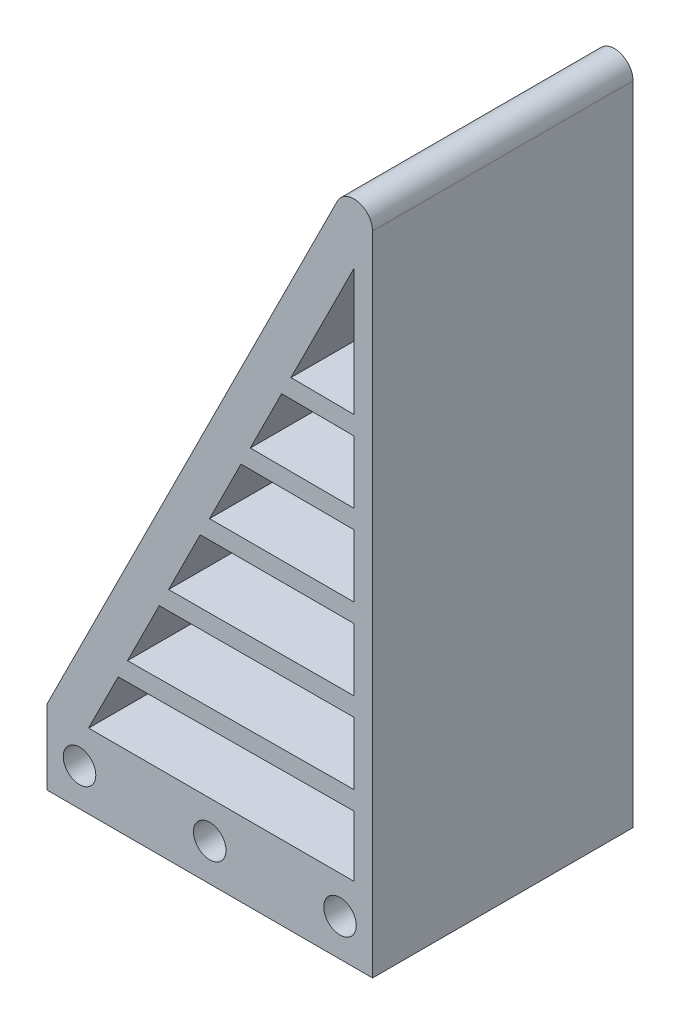
SolidWorks part; units mm, degrees
ref_plane "Спереди" through (0, 0, 0) normal (0, 0, 1) x (1, 0, 0)
ref_plane "Сверху" through (0, 0, 0) normal (0, 1, 0) x (1, 0, 0)
ref_plane "Справа" through (0, 0, 0) normal (1, 0, 0) x (0, 0, -1)
other "Configuration Table"
sketch "Эскиз1" plane through (0, 0, 0) normal (0, 0, 1) x (1, 0, 0)
  line L0 (17.5, 4) -> (17.5, 74)
  line L1 (-17.5, -4) -> (17.5, -4)
  line L2 (-17.5, -4) -> (-17.5, 4)
  line L3 (-17.5, 4) -> (17.5, 4)
  line L4 (17.5, -4) -> (17.5, 4)
  line L5 (-17.5, -4) -> (17.5, 4) construction
  line L6 (-17.5, 4) -> (17.5, -4) construction
  line L7 (17.5, 74) -> (-17.5, 4)
  point P0 (0, 0)
  dimension "D1" = 35
  dimension "D2" = 8
  dimension "D3" = 70
extrude "Бобышка-Вытянуть1" add sketch "Эскиз1" along normal blind 28 contours L0 L7 L3 | L1 L4 L3 L2
sketch "Эскиз2" plane through (0, 0, 28) normal (0, 0, 1) x (1, 0, 0)
  line L0 (-17.5, 0) -> (17.5, 0) construction
  line L1 (-17.5, -4) -> (-17.5, 4) construction
  line L2 (17.5, -4) -> (17.5, 74) construction
  circle A0 centre (0, 0) radius 1.75
  circle A1 centre (-14, 0) radius 1.75
  circle A2 centre (14, 0) radius 1.75
  dimension "D3" = 3.5
  dimension "D1" = 14
  dimension "D2" = 14
extrude "Вырез-Вытянуть1" cut sketch "Эскиз2" against normal through all
sketch "Эскиз3" plane through (0, 0, 28) normal (0, 0, 1) x (1, 0, 0)
  line L0 (-17.5, 4) -> (17.5, 4) construction
  line L1 (17.5, -4) -> (17.5, 74) construction
  line L2 (17.5, 4) -> (17.5, 74) construction
  line L3 (-13.0279, 4) -> (15.5, 4)
  line L4 (15.5, 4) -> (15.5, 61.0557)
  line L5 (15.5, 61.0557) -> (-13.0279, 4)
  line L6 (17.5, 74) -> (-17.5, 4) construction
  dimension "D1" = 70
  dimension "D2" = 35
  dimension "D3" = 2
  dimension "D4" = 4
extrude "Вырез-Вытянуть2" cut sketch "Эскиз3" against normal through all
fillet "Скругление1" radius 2 1 edges at (17.5, 74, 14)
sketch "Эскиз5" plane through (0, 0, 28) normal (0, 0, 1) x (1, 0, 0)
  line L0 (15.5, 4) -> (17.5, 4) construction
  line L1 (17.5, -4) -> (17.5, 65.5279) construction
  line L2 (16.5, 4) -> (2516.5, 4) construction
  line L3 (2516.5, 4) -> (2516.5, 29) construction
  line L4 (2405.754, 29.7732) -> (-47593.0275, 378.8362) construction
  line L5 (2397.8721, 29.4141) -> (-47601.8233, 203.9467) construction
  line L6 (2405.8253, 28.2273) -> (-47592.9563, -320.8357) construction
  line L7 (2405.8034, 28.6136) -> (-47593.892, -145.919) construction
  line L8 (1405.7842, 29) -> (51405.7842, 29) construction
  line L9 (15.5, 12.5395) -> (15.5, 10.5394)
  line L10 (15.5, 4) -> (15.5, 61.0557) construction
  line L11 (15.5, 10.5394) -> (-9.8466, 10.3625)
  line L12 (15.5, 61.0557) -> (-13.0279, 4) construction
  line L13 (-9.8466, 10.3625) -> (-8.8431, 12.3695)
  line L14 (-8.8431, 12.3695) -> (15.5, 12.5395)
  line L15 (15.5, 21.2698) -> (15.5, 19.2698)
  line L16 (15.5, 19.2698) -> (-5.4295, 19.1968)
  line L17 (-5.4295, 19.1968) -> (-4.4277, 21.2003)
  line L18 (-4.4277, 21.2003) -> (15.5, 21.2698)
  line L19 (-0.0279, 30) -> (-1.0279, 28)
  line L20 (-1.0279, 28) -> (15.5, 28)
  line L21 (15.5, 28) -> (15.5, 30)
  line L22 (15.5, 30) -> (-0.0279, 30)
  line L23 (4.3567, 38.7691) -> (3.3584, 36.7725)
  line L24 (3.3584, 36.7725) -> (15.5, 36.7302)
  line L25 (15.5, 36.7302) -> (15.5, 38.7302)
  line L26 (15.5, 38.7302) -> (4.3567, 38.7691)
  line L27 (8.7261, 47.5079) -> (7.7295, 45.5148)
  line L28 (7.7295, 45.5148) -> (15.5, 45.4605)
  line L29 (15.5, 45.4605) -> (15.5, 47.4606)
  line L30 (15.5, 47.4606) -> (8.7261, 47.5079)
  dimension "D1" = 2500
  dimension "D2" = 25
  dimension "D3" = 0.2
  dimension "D4" = 0.4
  dimension "D5" = 0.2
  dimension "D6" = 0.4
  dimension "D7" = 2
  dimension "D8" = 2
  dimension "D9" = 2
  dimension "D10" = 2
  dimension "D11" = 2
extrude "Бобышка-Вытянуть2" add sketch "Эскиз5" against normal up to surface (28 mm away) up to face at (5.9907, 23.0186, 0)
